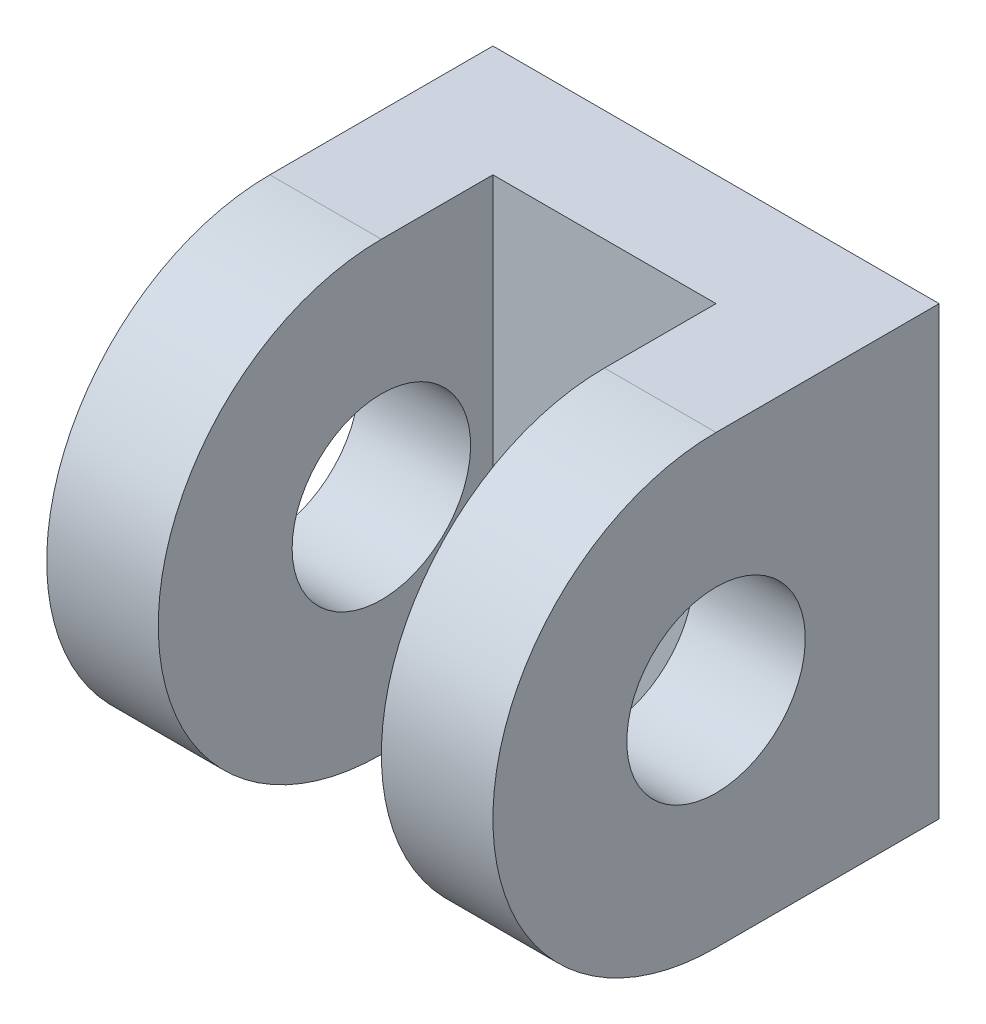
SolidWorks part; units mm, degrees
ref_plane "Front Plane" through (0, 0, 0) normal (0, 0, 1) x (1, 0, 0)
ref_plane "Top Plane" through (0, 0, 0) normal (0, 1, 0) x (1, 0, 0)
ref_plane "Right Plane" through (0, 0, 0) normal (1, 0, 0) x (0, 0, -1)
sketch "Sketch1" plane through (0, 0, 0) normal (0, 0, 1) x (1, 0, 0)
  line L0 (0, 0) -> (0, 20)
  line L1 (0, 20) -> (20, 20)
  line L2 (20, 20) -> (20, 0)
  line L3 (20, 0) -> (0, 0)
  point P5 (28.0388, 0)
  dimension "D1" = 20
  dimension "D2" = 20
extrude "Boss-Extrude1" add sketch "Sketch1" along normal blind 5
sketch "Sketch2" plane through (0, 0, 5) normal (0, 0, 1) x (1, 0, 0)
  line L0 (0, 20) -> (0, 0)
  line L1 (0, 0) -> (5, 0)
  line L2 (0, 0) -> (20, 0) construction
  line L3 (5, 0) -> (5, 20)
  line L4 (20, 20) -> (0, 20) construction
  line L5 (5, 20) -> (0, 20)
  line L6 (20, 20) -> (20, 0)
  line L7 (20, 0) -> (15, 0)
  line L8 (15, 0) -> (15, 20)
  line L9 (15, 20) -> (20, 20)
  dimension "D1" = 5
  dimension "D2" = 5
extrude "Boss-Extrude2" add sketch "Sketch2" along normal blind 5
sketch "Sketch3" plane through (20, 0, 0) normal (1, 0, 0) x (0, 0, -1)
  line L0 (-10, 0) -> (-10, 20) construction
  circle A0 centre (-10, 10) radius 10
  point P2 (0, 0)
extrude "Boss-Extrude5" add sketch "Sketch3" against normal blind 5
sketch "Sketch6" plane through (0, 0, 0) normal (-1, 0, 0) x (0, 0, 1)
  line L0 (10, 20) -> (10, 0) construction
  circle A0 centre (10, 10) radius 10
  point P2 (0, 0)
extrude "Boss-Extrude6" add sketch "Sketch6" against normal blind 5 contours A0
sketch "Sketch5" plane through (20, 0, 0) normal (1, 0, 0) x (0, 0, -1)
  line L0 (-10, 0) -> (-10, 20) construction
  line L1 (3.6996, 10) -> (-9.9175, 10) construction
  circle A0 centre (-10, 10) radius 4
  point P7 (0, 0)
  point P9 (0, 0)
  dimension "D1" = 8
extrude "Cut-Extrude1" cut sketch "Sketch5" against normal through all contours A0
